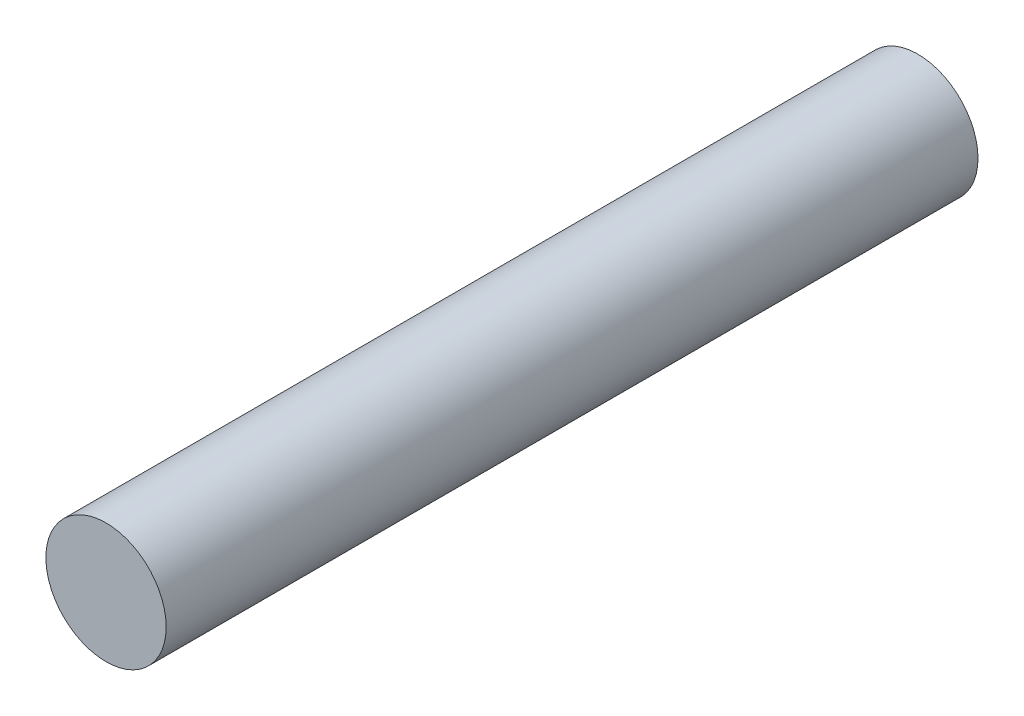
SolidWorks part; units mm, degrees
ref_plane "Front Plane" through (0, 0, 0) normal (0, 0, 1) x (1, 0, 0)
ref_plane "Top Plane" through (0, 0, 0) normal (0, 1, 0) x (1, 0, 0)
ref_plane "Right Plane" through (0, 0, 0) normal (1, 0, 0) x (0, 0, -1)
sketch "Sketch1" plane through (0, 0, 0) normal (0, 0, 1) x (1, 0, 0)
  circle A0 centre (-52.8203, 32.8843) radius 4
extrude "Boss-Extrude1" add sketch "Sketch1" along normal blind 54
